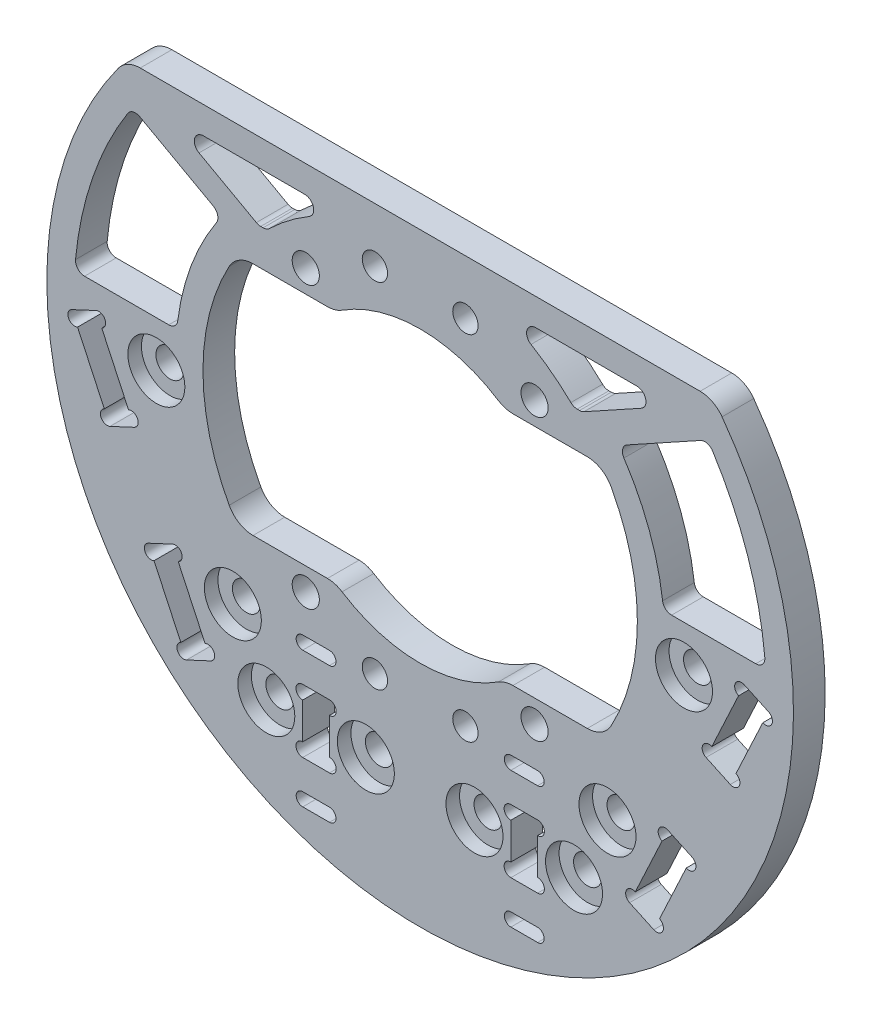
SolidWorks part; units mm, degrees
ref_plane "前视基准面" through (0, 0, 0) normal (0, 0, 1) x (1, 0, 0)
ref_plane "上视基准面" through (0, 0, 0) normal (0, 1, 0) x (1, 0, 0)
ref_plane "右视基准面" through (0, 0, 0) normal (1, 0, 0) x (0, 0, -1)
sketch "草图1" plane through (0, 0, 0) normal (0, 0, 1) x (1, 0, 0)
  line L0 (-32.4239, 25.5) -> (32.4239, 25.5)
  line L1 (12.6392, -15.5) -> (-12.6392, -15.5) construction
  line L2 (12.6392, -15.5) -> (12.6392, 15.5) construction
  line L3 (12.6392, 15.5) -> (-12.6392, 15.5) construction
  line L4 (-12.6392, -15.5) -> (-12.6392, 15.5) construction
  line L5 (12.6392, -15.5) -> (-12.6392, 15.5) construction
  line L6 (12.6392, 15.5) -> (-12.6392, -15.5) construction
  line L11 (-20.1742, 13) -> (-9.3274, 13)
  line L12 (-20.1742, -13) -> (-9.3274, -13)
  line L13 (9.3274, 13) -> (20.1742, 13)
  line L14 (9.3274, -13) -> (20.1742, -13)
  circle A0 centre (0, 0) radius 24 construction
  circle A1 centre (-12.6392, 15.5) radius 4 construction
  circle A2 centre (-12.6392, 15.5) radius 1.5
  circle A3 centre (-12.6392, -15.5) radius 1.5
  circle A4 centre (12.6392, -15.5) radius 1.5
  circle A5 centre (12.6392, 15.5) radius 1.5
  arc A6 (-32.4239, 25.5) -> (32.4239, 25.5) centre (0, 0) ccw
  arc A8 (-9.3274, -13) -> (9.3274, -13) centre (0, 0) ccw
  arc A9 (-20.1742, 13) -> (-20.1742, -13) centre (0, 0) ccw
  arc A10 (20.1742, 13) -> (20.1742, -13) centre (0, 0) cw
  arc A11 (9.3274, 13) -> (-9.3274, 13) centre (0, 0) ccw
  dimension "D1" = 31
  dimension "D2" = 48
  dimension "D3" = 8
  dimension "D4" = 3
  dimension "D7" = 32
  dimension "D5" = 82.5
  dimension "D6" = 10
  dimension "D8" = 26
extrude "凸台-拉伸1" add sketch "草图1" along normal mid plane 3.5
fillet "圆角2" radius 3 8 edges at (20.1742, -13, 0) (20.1742, 13, 0) (-20.1742, -13, 0) (-9.3274, -13, 0) (9.3274, -13, 0) (9.3274, 13, 0) (-9.3274, 13, 0) (-20.1742, 13, 0)
fillet "圆角3" radius 3 2 edges at (-32.4239, 25.5, 0) (32.4239, 25.5, 0)
sketch "草图2" plane through (0, 0, -1.75) normal (0, 0, -1) x (-1, 0, 0)
  line L0 (0, 16) -> (0, -16) construction
  line L1 (-29.1496, -2.5589) -> (-20.6973, -20.6851) construction
  line L2 (35.8169, -0.151) -> (38.4905, -1.3978)
  line L3 (-31.5908, -9.2141) -> (-34.2644, -10.4608)
  line L4 (-31.5908, -9.2141) -> (-35.8169, -0.151)
  line L5 (-35.8169, -0.151) -> (-38.4905, -1.3978)
  line L6 (-34.2644, -10.4608) -> (-38.4905, -1.3978)
  line L7 (-31.5908, -9.2141) -> (-38.4905, -1.3978) construction
  line L8 (-35.8169, -0.151) -> (-34.2644, -10.4608) construction
  line L9 (34.2644, -10.4608) -> (38.4905, -1.3978)
  line L10 (31.5908, -9.2141) -> (34.2644, -10.4608)
  line L11 (31.5908, -9.2141) -> (35.8169, -0.151)
  line L12 (-30.9324, 25.5) -> (30.9324, 25.5) construction
  line L17 (-23.1384, -27.3403) -> (-25.812, -28.587)
  line L18 (-30.0382, -19.5239) -> (-25.812, -28.587)
  line L19 (-27.3646, -18.2772) -> (-30.0382, -19.5239)
  line L20 (-27.3646, -18.2772) -> (-23.1384, -27.3403)
  line L21 (-30.0382, -19.5239) -> (-23.1384, -27.3403) construction
  line L22 (-25.812, -28.587) -> (-27.3646, -18.2772) construction
  line L23 (-35.0406, -5.3059) -> (-26.5883, -23.4321) construction
  line L24 (27.3646, -18.2772) -> (23.1384, -27.3403)
  line L25 (27.3646, -18.2772) -> (30.0382, -19.5239)
  line L26 (30.0382, -19.5239) -> (25.812, -28.587)
  line L27 (23.1384, -27.3403) -> (25.812, -28.587)
  line L28 (-30.8145, -14.369) -> (0, 0) construction
  circle A1 centre (-29.1496, -2.5589) radius 1.55
  circle A2 centre (-20.6973, -20.6851) radius 1.55
  arc A3 (8.629, 13.4737) -> (-8.629, 13.4737) centre (0, 0) ccw construction
  arc A4 (-8.629, -13.4737) -> (8.629, -13.4737) centre (0, 0) ccw construction
  circle A5 centre (20.6973, -20.6851) radius 1.55
  circle A6 centre (29.1496, -2.5589) radius 1.55
  point P1 (-24.9235, -11.622)
  dimension "D1" = 20
  dimension "D2" = 3.1
  dimension "D3" = 65
  dimension "D4" = 2.95
  dimension "D8" = 27.5
  dimension "D7" = 34
  dimension "D5" = 20
  dimension "D6" = 10
extrude "切除-拉伸1" cut sketch "草图2" against normal through all
sketch "草图3" plane through (0, 0, 1.75) normal (0, 0, 1) x (1, 0, 0)
  circle A0 centre (-29.1496, -2.5589) radius 3.15
  circle A1 centre (-20.6973, -20.6851) radius 3.15
  circle A2 centre (29.1496, -2.5589) radius 3.15
  circle A3 centre (20.6973, -20.6851) radius 3.15
  dimension "D1" = 6.3
extrude "切除-拉伸2" cut sketch "草图3" against normal blind 1.5
sketch "草图4" plane through (0, 0, -1.75) normal (0, 0, -1) x (-1, 0, 0)
  line L0 (-31.5908, -9.2141) -> (-35.8169, -0.151) construction
  line L1 (-38.4905, -1.3978) -> (-34.2644, -10.4608) construction
  line L2 (35.8169, -0.151) -> (31.5908, -9.2141) construction
  line L3 (34.2644, -10.4608) -> (38.4905, -1.3978) construction
  line L4 (-30.0382, -19.5239) -> (-25.812, -28.587) construction
  line L5 (-23.1384, -27.3403) -> (-27.3646, -18.2772) construction
  line L6 (27.3646, -18.2772) -> (23.1384, -27.3403) construction
  line L7 (25.812, -28.587) -> (30.0382, -19.5239) construction
  circle A0 centre (-35.5, -0.8308) radius 0.75
  circle A1 centre (-31.9077, -8.5344) radius 0.75
  circle A2 centre (-34.5813, -9.7811) radius 0.75
  circle A3 centre (-38.1736, -2.0775) radius 0.75
  circle A4 centre (35.5, -0.8308) radius 0.75
  circle A5 centre (38.1736, -2.0775) radius 0.75
  circle A6 centre (31.9077, -8.5344) radius 0.75
  circle A7 centre (34.5813, -9.7811) radius 0.75
  circle A8 centre (-29.7212, -20.2037) radius 0.75
  circle A9 centre (-27.0476, -18.9569) radius 0.75
  circle A10 centre (-26.129, -27.9073) radius 0.75
  circle A11 centre (-23.4554, -26.6605) radius 0.75
  circle A12 centre (23.4554, -26.6605) radius 0.75
  circle A13 centre (26.129, -27.9073) radius 0.75
  circle A14 centre (27.0476, -18.9569) radius 0.75
  circle A15 centre (29.7212, -20.2037) radius 0.75
  dimension "D1" = 1.5
extrude "切除-拉伸3" cut sketch "草图4" against normal through all
sketch "草图5" plane through (0, 0, -1.75) normal (0, 0, -1) x (-1, 0, 0)
  line L1 (5, -19.5) -> (-5, -19.5) construction
  line L2 (5, -19.5) -> (5, 19.5) construction
  line L3 (5, 19.5) -> (-5, 19.5) construction
  line L4 (-5, -19.5) -> (-5, 19.5) construction
  line L5 (5, -19.5) -> (-5, 19.5) construction
  line L6 (5, 19.5) -> (-5, -19.5) construction
  circle A0 centre (-5, 19.5) radius 1.4
  circle A1 centre (5, 19.5) radius 1.4
  circle A2 centre (-5, -19.5) radius 1.4
  circle A3 centre (5, -19.5) radius 1.4
  point P0 (0, 0)
  dimension "D1" = 10
  dimension "D3" = 2.8
  dimension "D2" = 39
extrude "切除-拉伸4" cut sketch "草图5" against normal through all
sketch "草图6" plane through (0, 0, -1.75) normal (0, 0, -1) x (-1, 0, 0)
  line L0 (-20.9762, 17) -> (-16.9411, 17)
  line L2 (-30.9324, 22.5) -> (-8.3516, 22.5)
  line L3 (-30.9324, 25.5) -> (30.9324, 25.5) construction
  line L4 (0, 16) -> (0, -16) construction
  line L7 (-18.4662, 13) -> (-10.247, 13) construction
  line L8 (-38.1682, 2.5) -> (-26.884, 2.5)
  line L9 (38.1682, 2.5) -> (26.884, 2.5)
  line L10 (30.9324, 22.5) -> (8.3516, 22.5)
  line L11 (20.9762, 17) -> (16.9411, 17)
  arc A0 (-8.3516, 22.5) -> (-16.9411, 17) centre (0, 0) ccw
  arc A1 (8.629, 13.4737) -> (-8.629, 13.4737) centre (0, 0) ccw construction
  arc A2 (-30.9324, 22.5) -> (-38.1682, 2.5) centre (0, 0) ccw
  arc A3 (-33.3585, 24.2647) -> (33.3585, 24.2647) centre (0, 0) ccw construction
  arc A4 (-8.629, -13.4737) -> (8.629, -13.4737) centre (0, 0) ccw construction
  arc A8 (-20.9762, 17) -> (-26.884, 2.5) centre (0, 0) ccw
  arc A9 (-21.1042, 11.4286) -> (-21.1042, -11.4286) centre (0, 0) ccw construction
  arc A10 (20.9762, 17) -> (26.884, 2.5) centre (0, 0) cw
  arc A11 (30.9324, 22.5) -> (38.1682, 2.5) centre (0, 0) cw
  arc A12 (8.3516, 22.5) -> (16.9411, 17) centre (0, 0) cw
  dimension "D1" = 8
  dimension "D2" = 3
  dimension "D5" = 3
  dimension "D3" = 4
  dimension "D4" = 3
  dimension "D6" = 20
extrude "切除-拉伸5" cut sketch "草图6" against normal through all
sketch "草图7" plane through (0, 0, -1.75) normal (0, 0, -1) x (-1, 0, 0)
  line L0 (-30.9324, 22.5) -> (-20.9762, 17) construction
  line L1 (-31.7954, 21.2631) -> (-21.8976, 15.7954)
  line L2 (-27.8303, 22.5) -> (-17.8741, 17)
  line L3 (-8.3516, 22.5) -> (-30.9324, 22.5) construction
  line L4 (-20.9762, 17) -> (-16.9411, 17) construction
  line L5 (-27.8303, 22.5) -> (-30.9324, 22.5)
  line L6 (-20.9762, 17) -> (-17.8741, 17)
  line L7 (-31.6577, 21.187) -> (-21.7015, 15.687) construction
  line L8 (-30.2071, 23.813) -> (-20.2509, 18.313) construction
  line L9 (0, 16) -> (0, 25.5) construction
  line L10 (-30.9324, 25.5) -> (30.9324, 25.5) construction
  line L11 (27.8303, 22.5) -> (30.9324, 22.5)
  line L12 (27.8303, 22.5) -> (17.8741, 17)
  line L13 (20.9762, 17) -> (17.8741, 17)
  line L14 (31.7954, 21.2631) -> (21.8976, 15.7954)
  arc A0 (-30.9324, 22.5) -> (-38.1682, 2.5) centre (0, 0) ccw construction
  arc A2 (-30.9324, 22.5) -> (-31.7954, 21.2631) centre (0, 0) ccw
  arc A5 (-20.9762, 17) -> (-26.884, 2.5) centre (0, 0) ccw construction
  arc A6 (-20.9762, 17) -> (-21.8976, 15.7954) centre (0, 0) ccw
  arc A7 (8.629, 13.4737) -> (-8.629, 13.4737) centre (0, 0) ccw construction
  arc A8 (30.9324, 22.5) -> (31.7954, 21.2631) centre (0, 0) cw
  arc A9 (20.9762, 17) -> (21.8976, 15.7954) centre (0, 0) cw
  dimension "D1" = 1.5
  dimension "D2" = 1.5
extrude "凸台-拉伸2" add sketch "草图7" against normal blind 3.5
fillet "圆角5" radius 1 16 edges at (-31.7954, 21.2631, 0) (-26.884, 2.5, 0) (-21.8976, 15.7954, 0) (-38.1682, 2.5, 0) (-16.9411, 17, 0) (-8.3516, 22.5, 0) (-27.8303, 22.5, 0) (-17.8741, 17, 0) (27.8303, 22.5, 0) (8.3516, 22.5, 0) (17.8741, 17, 0) (16.9411, 17, 0) (26.884, 2.5, 0) (38.1682, 2.5, 0) (31.7954, 21.2631, 0) (21.8976, 15.7954, 0)
sketch "草图8" plane through (0, 0, -1.75) normal (0, 0, -1) x (-1, 0, 0)
  line L0 (0, -16) -> (0, -41.25) construction
  line L1 (10.025, -24.5) -> (12.975, -24.5)
  line L2 (-10.025, -31.5) -> (-12.975, -31.5)
  line L3 (-10.025, -31.5) -> (-10.025, -24.5)
  line L4 (-10.025, -24.5) -> (-12.975, -24.5)
  line L5 (-12.975, -31.5) -> (-12.975, -24.5)
  line L6 (-10.025, -31.5) -> (-12.975, -24.5) construction
  line L7 (-10.025, -24.5) -> (-12.975, -31.5) construction
  line L8 (12.975, -31.5) -> (12.975, -24.5)
  line L9 (10.025, -31.5) -> (12.975, -31.5)
  line L10 (10.025, -31.5) -> (10.025, -24.5)
  line L11 (-11.5, -28) -> (0, -28) construction
  line L12 (-10.025, -21.225) -> (-12.975, -21.225)
  line L13 (-10.025, -21.225) -> (-10.025, -19.775)
  line L14 (-10.025, -19.775) -> (-12.975, -19.775)
  line L15 (-12.975, -21.225) -> (-12.975, -19.775)
  line L16 (-10.025, -21.225) -> (-12.975, -19.775) construction
  line L17 (-10.025, -19.775) -> (-12.975, -21.225) construction
  line L22 (-10.025, -36.225) -> (-12.975, -36.225)
  line L23 (-12.975, -34.775) -> (-12.975, -36.225)
  line L24 (-10.025, -34.775) -> (-12.975, -34.775)
  line L25 (-10.025, -34.775) -> (-10.025, -36.225)
  line L26 (10.025, -34.775) -> (10.025, -36.225)
  line L27 (10.025, -34.775) -> (12.975, -34.775)
  line L28 (12.975, -34.775) -> (12.975, -36.225)
  line L29 (10.025, -36.225) -> (12.975, -36.225)
  line L30 (10.025, -19.775) -> (12.975, -19.775)
  line L31 (12.975, -21.225) -> (12.975, -19.775)
  line L32 (10.025, -21.225) -> (12.975, -21.225)
  line L33 (10.025, -21.225) -> (10.025, -19.775)
  arc A0 (-8.629, -13.4737) -> (8.629, -13.4737) centre (0, 0) ccw construction
  arc A1 (-33.3585, 24.2647) -> (33.3585, 24.2647) centre (0, 0) ccw construction
  circle A2 centre (-17, -28) radius 4.025 construction
  circle A3 centre (-6, -28) radius 4.025 construction
  circle A4 centre (-17, -28) radius 1.55
  circle A5 centre (-6, -28) radius 1.55
  circle A6 centre (6, -28) radius 1.55
  circle A7 centre (17, -28) radius 1.55
  point P8 (-11.5, -28)
  point P32 (-11.5, -20.5)
  dimension "D5" = 11
  dimension "D6" = 3.1
  dimension "D7" = 15
  dimension "D1" = 23
  dimension "D2" = 2.95
  dimension "D3" = 7
  dimension "D4" = 28
  dimension "D8" = 1.45
extrude "切除-拉伸6" cut sketch "草图8" against normal through all
sketch "草图9" plane through (0, 0, -1.75) normal (0, 0, -1) x (-1, 0, 0)
  line L0 (-12.975, -24.5) -> (-12.975, -31.5) construction
  line L1 (-10.025, -31.5) -> (-10.025, -24.5) construction
  line L2 (10.025, -24.5) -> (10.025, -31.5) construction
  line L3 (12.975, -31.5) -> (12.975, -24.5) construction
  line L18 (-10.025, -21.225) -> (-10.025, -19.775) construction
  line L19 (-12.975, -19.775) -> (-12.975, -21.225) construction
  line L20 (-10.025, -36.225) -> (-10.025, -34.775) construction
  line L21 (-12.975, -34.775) -> (-12.975, -36.225) construction
  line L22 (12.975, -21.225) -> (12.975, -19.775) construction
  line L23 (10.025, -19.775) -> (10.025, -21.225) construction
  line L24 (12.975, -36.225) -> (12.975, -34.775) construction
  line L25 (10.025, -34.775) -> (10.025, -36.225) construction
  circle A0 centre (-12.975, -25.25) radius 0.75
  circle A1 centre (-10.025, -25.25) radius 0.75
  circle A2 centre (-12.975, -30.75) radius 0.75
  circle A3 centre (-10.025, -30.75) radius 0.75
  circle A4 centre (10.025, -25.25) radius 0.75
  circle A5 centre (12.975, -25.25) radius 0.75
  circle A6 centre (10.025, -30.75) radius 0.75
  circle A7 centre (12.975, -30.75) radius 0.75
  circle A24 centre (-10.025, -20.5) radius 0.725
  circle A25 centre (-12.975, -20.5) radius 0.725
  circle A26 centre (-10.025, -35.5) radius 0.725
  circle A27 centre (-12.975, -35.5) radius 0.725
  circle A28 centre (12.975, -20.5) radius 0.725
  circle A29 centre (10.025, -20.5) radius 0.725
  circle A30 centre (12.975, -35.5) radius 0.725
  circle A31 centre (10.025, -35.5) radius 0.725
  dimension "D1" = 1.5
extrude "切除-拉伸7" cut sketch "草图9" against normal through all
sketch "草图12" plane through (0, 0, 1.75) normal (0, 0, 1) x (1, 0, 0)
  circle A0 centre (-17, -28) radius 3.15
  circle A1 centre (17, -28) radius 3.15
  circle A2 centre (-6, -28) radius 3.15
  circle A3 centre (6, -28) radius 3.15
  circle A4 centre (-20.6973, -20.6851) radius 3.15 construction
extrude "切除-拉伸8" cut sketch "草图12" against normal up to surface (1.5 mm away) up to face at (-17.5473, -20.6851, 0.25)
